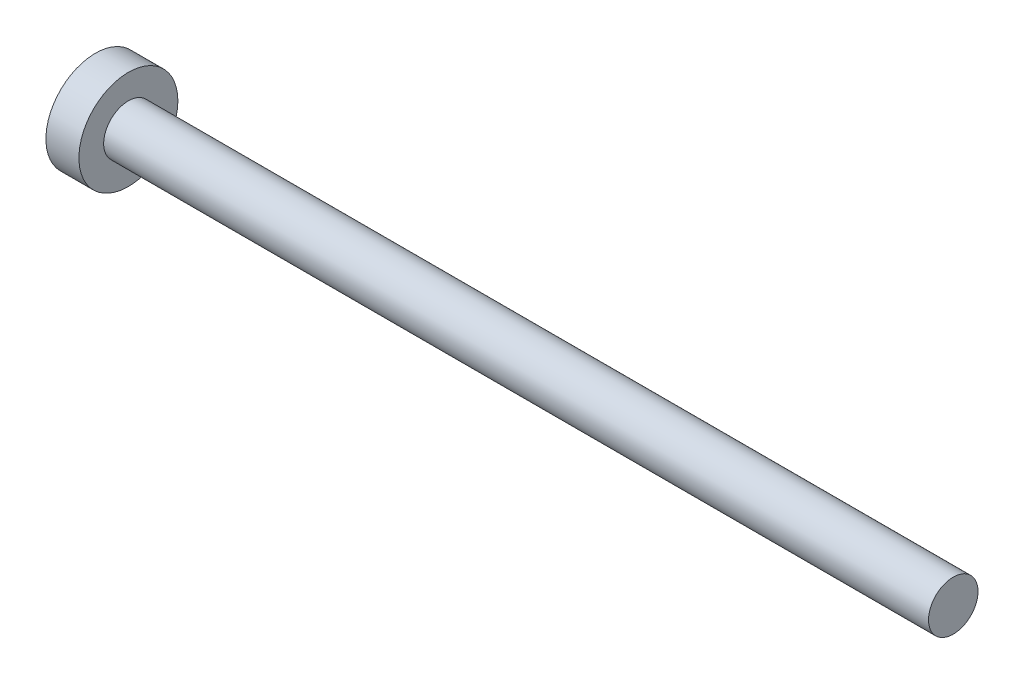
SolidWorks part; units mm, degrees
ref_plane "Front Plane" through (0, 0, 0) normal (0, 0, 1) x (1, 0, 0)
ref_plane "Top Plane" through (0, 0, 0) normal (0, 1, 0) x (1, 0, 0)
ref_plane "Right Plane" through (0, 0, 0) normal (1, 0, 0) x (0, 0, -1)
sketch "Sketch1" plane through (0, 0, 0) normal (1, 0, 0) x (0, 0, -1)
  circle A0 centre (0, 0) radius 3
  dimension "D1" = 6
extrude "Boss-Extrude1" add sketch "Sketch1" along normal blind 2
sketch "Sketch2" plane through (2, 0, 0) normal (1, 0, 0) x (0, 0, -1)
  circle A0 centre (0, 0) radius 1.5
  dimension "D1" = 3
extrude "Boss-Extrude2" add sketch "Sketch2" along normal blind 50
